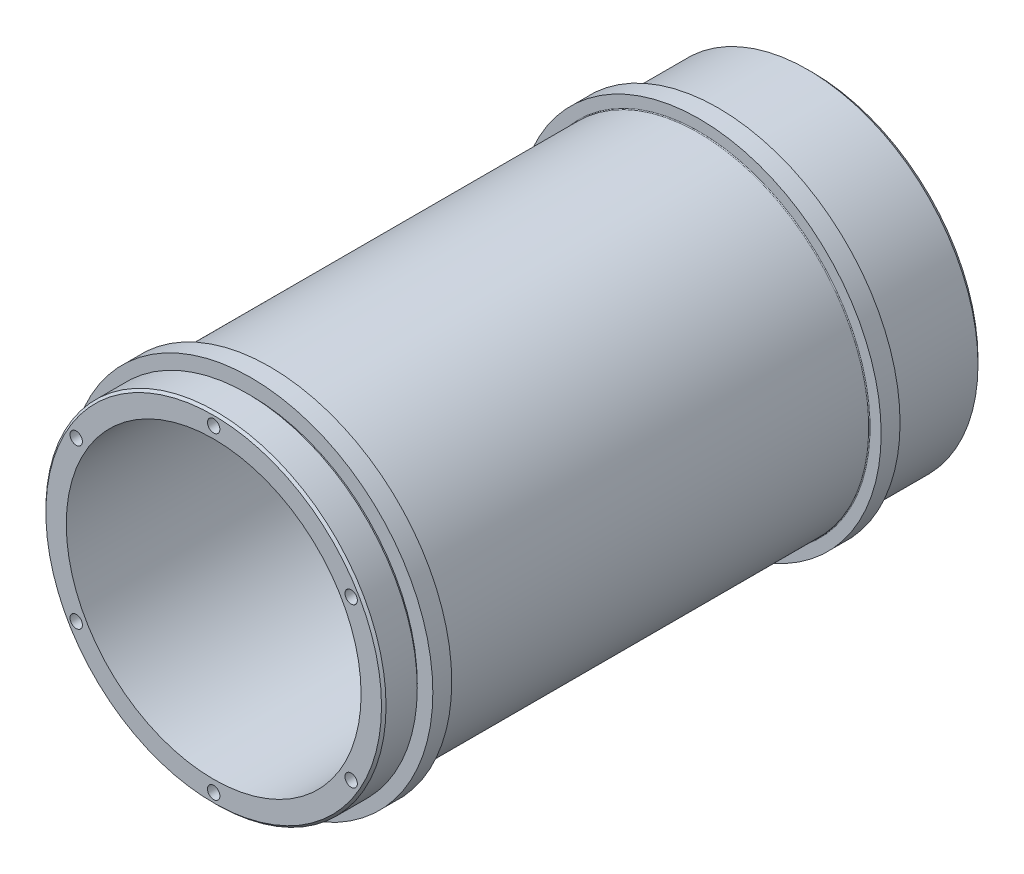
SolidWorks part; units mm, degrees
ref_plane "Front Plane" through (0, 0, 0) normal (0, 0, 1) x (1, 0, 0)
ref_plane "Top Plane" through (0, 0, 0) normal (0, 1, 0) x (1, 0, 0)
ref_plane "Right Plane" through (0, 0, 0) normal (1, 0, 0) x (0, 0, -1)
sketch "Sketch1" plane through (0, 0, 0) normal (0, 0, 1) x (1, 0, 0)
  circle A0 centre (0, 0) radius 57.15
  dimension "D1" = 114.3
extrude "Boss-Extrude1" add sketch "Sketch1" along normal blind 201.2442
ref_plane "Plane1" through (0, 0, 201.2442) normal (0, 0, 1) x (1, 0, 0)
sketch "Sketch3" plane through (0, 0, 0) normal (1, 0, 0) x (0, 0, -1)
  line L0 (0, 57.15) -> (-201.2442, 57.15) construction
  line L1 (-31.75, 57.15) -> (-30.48, 57.15)
  line L2 (-31.75, 57.15) -> (-31.75, 55.88)
  line L3 (-31.75, 55.88) -> (-30.48, 55.88)
  line L4 (-30.48, 57.15) -> (-30.48, 55.88)
  line L5 (0, 55) -> (0, -55) construction
  line L7 (-189.992, 57.15) -> (-188.722, 57.15)
  line L8 (-189.992, 57.15) -> (-189.992, 55.88)
  line L9 (-189.992, 55.88) -> (-188.722, 55.88)
  line L10 (-188.722, 57.15) -> (-188.722, 55.88)
  line L11 (-212.826, 0) -> (0, 0) construction
  dimension "D1" = 1.27
  dimension "D2" = 1.27
  dimension "D3" = 31.75
  dimension "D4" = 1.27
  dimension "D5" = 1.27
  dimension "D6" = 156.972
revolve "Cut-Revolve2" cut sketch "Sketch3" angle 360 about L11
ref_plane "Plane4" through (0, 0, 188.722) normal (0, 0, 1) x (1, 0, 0)
sketch "Sketch9" plane through (0, 0, 188.722) normal (0, 0, 1) x (1, 0, 0)
  circle A0 centre (0, 0) radius 61.1124
  dimension "D1" = 122.2248
extrude "Boss-Extrude4" add sketch "Sketch9" against normal blind 6.35
ref_plane "Plane5" through (0, 0, 31.75) normal (0, 0, -1) x (-1, 0, 0)
sketch "Sketch10" plane through (0, 0, 31.75) normal (0, 0, -1) x (-1, 0, 0)
  circle A0 centre (0, 0) radius 61.1124
extrude "Boss-Extrude5" add sketch "Sketch10" against normal blind 6.35
hole_wizard "#97 (0.164) Diameter Hole1" positions "Sketch11" profile "Sketch12" hole size "#97" standard "ANSI Inch"
sketch "Sketch11" plane through (0, 0, 201.2442) normal (0, 0, 1) x (1, 0, 0)
  line L0 (0, -62.865) -> (0, 62.865) construction
  point P0 (0, 53.34)
  point P12 (46.1938, 26.67)
  point P13 (46.1938, -26.67)
  point P14 (0, -53.34)
  point P15 (-46.1938, -26.67)
  point P16 (-46.1938, 26.67)
  point P18 (0, 0)
  dimension "D1" = 53.34
  dimension "D2" = 6
sketch "Sketch12" plane through (0, 53.34, 201.2442) normal (1, 0, 0) x (0, -1, 0)
  line L0 (0, 0) -> (0, 9.5065)
  line L1 (0, 9.5065) -> (2.0828, 8.255)
  line L2 (2.0828, 8.255) -> (2.0828, 0)
  line L5 (2.0828, 0) -> (0, 0)
  line L10 (0, 9.5065) -> (-2.0828, 8.255) construction
  line L11 (0, -6.35) -> (0, 107.95) construction
  dimension "Hole Dia." = 4.1656
  dimension "Hole Depth" = 8.255
  dimension "Drill Angle" = 118
hole_wizard "#97 (0.352) Diameter Hole1" positions "Sketch16" profile "Sketch17" hole size "#97" standard "ANSI Inch" end condition through all
sketch "Sketch16" plane through (0, 0, 201.2442) normal (0, 0, 1) x (1, 0, 0)
  line L0 (0, -62.865) -> (0, 62.865) construction
  line L1 (62.865, 0) -> (-62.865, 0) construction
  point P9 (0, 38.735)
  point P20 (33.5455, 19.3675)
  point P21 (33.5455, -19.3675)
  point P22 (0, -38.735)
  point P23 (-33.5455, -19.3675)
  point P24 (-33.5455, 19.3675)
  point P30 (0, 0)
  dimension "D1" = 38.735
  dimension "D2" = 6
sketch "Sketch17" plane through (0, 38.735, 201.2442) normal (1, 0, 0) x (0, -1, 0)
  line L0 (0, 0) -> (0, 201.2442)
  line L1 (0, 201.2442) -> (4.4704, 201.2442)
  line L2 (4.4704, 201.2442) -> (4.4704, 0)
  line L5 (4.4704, 0) -> (0, 0)
  line L11 (0, -6.35) -> (0, 107.95) construction
  dimension "Thru Hole Dia." = 8.9408
  dimension "Thru Hole Depth" = 201.2442
sketch "Sketch18" plane through (0, 0, 201.2442) normal (0, 0, 1) x (1, 0, 0)
  line L0 (-915.5188, -528.575) -> (-33.5455, -19.3675) construction
  line L1 (62.865, 0) -> (-62.865, 0) construction
  line L2 (-3.3488, 10.4902) -> (70.9835, 10.4902) construction
  line L3 (0, 0) -> (59.0953, 34.1187) construction
  line L4 (0, 0) -> (112.8605, 0) construction
  line L5 (26.5798, 10.4902) -> (32.1193, 10.4902)
  line L6 (22.3747, 17.7737) -> (25.1444, 22.571)
  line L7 (26.5798, -10.4902) -> (32.1193, -10.4902)
  line L8 (22.3747, -17.7737) -> (25.1444, -22.571)
  line L9 (4.2051, -28.2639) -> (6.9749, -33.0612)
  line L10 (-4.2051, -28.2639) -> (-6.9749, -33.0612)
  line L11 (-22.3747, -17.7737) -> (-25.1444, -22.571)
  line L12 (-26.5798, -10.4902) -> (-32.1193, -10.4902)
  line L13 (-26.5798, 10.4902) -> (-32.1193, 10.4902)
  line L14 (-22.3747, 17.7737) -> (-25.1444, 22.571)
  line L15 (-4.2051, 28.2639) -> (-6.9749, 33.0612)
  line L16 (4.2051, 28.2639) -> (6.9749, 33.0612)
  arc A0 (26.5798, 10.4902) -> (22.3747, 17.7737) centre (0, 0) ccw
  arc A1 (38.735, 0) -> (38.4172, 4.952) centre (0, 0) ccw
  arc A2 (38.4172, 4.952) -> (32.1193, 10.4902) centre (32.1193, 4.1402) ccw
  arc A3 (19.3675, 33.5455) -> (23.4971, 30.7942) centre (0, 0) cw
  arc A4 (23.4971, 30.7942) -> (25.1444, 22.571) centre (19.6451, 25.746) cw
  arc A5 (38.735, 0) -> (38.4172, -4.952) centre (0, 0) cw
  arc A6 (38.4172, -4.952) -> (32.1193, -10.4902) centre (32.1193, -4.1402) cw
  arc A7 (22.3747, -17.7737) -> (26.5798, -10.4902) centre (0, 0) ccw
  arc A8 (23.4971, -30.7942) -> (25.1444, -22.571) centre (19.6451, -25.746) ccw
  arc A9 (19.3675, -33.5455) -> (23.4971, -30.7942) centre (0, 0) ccw
  arc A10 (19.3675, -33.5455) -> (14.92, -35.7462) centre (0, 0) cw
  arc A11 (14.92, -35.7462) -> (6.9749, -33.0612) centre (12.4741, -29.8862) cw
  arc A12 (-4.2051, -28.2639) -> (4.2051, -28.2639) centre (0, 0) ccw
  arc A13 (-14.92, -35.7462) -> (-6.9749, -33.0612) centre (-12.4741, -29.8862) ccw
  arc A14 (-19.3675, -33.5455) -> (-14.92, -35.7462) centre (0, 0) ccw
  arc A15 (-19.3675, -33.5455) -> (-23.4971, -30.7942) centre (0, 0) cw
  arc A16 (-23.4971, -30.7942) -> (-25.1444, -22.571) centre (-19.6451, -25.746) cw
  arc A17 (-26.5798, -10.4902) -> (-22.3747, -17.7737) centre (0, 0) ccw
  arc A18 (-38.4172, -4.952) -> (-32.1193, -10.4902) centre (-32.1193, -4.1402) ccw
  arc A19 (-38.735, 0) -> (-38.4172, -4.952) centre (0, 0) ccw
  arc A20 (-38.735, 0) -> (-38.4172, 4.952) centre (0, 0) cw
  arc A21 (-38.4172, 4.952) -> (-32.1193, 10.4902) centre (-32.1193, 4.1402) cw
  arc A22 (-22.3747, 17.7737) -> (-26.5798, 10.4902) centre (0, 0) ccw
  arc A23 (-23.4971, 30.7942) -> (-25.1444, 22.571) centre (-19.6451, 25.746) ccw
  arc A24 (-19.3675, 33.5455) -> (-23.4971, 30.7942) centre (0, 0) ccw
  arc A25 (-19.3675, 33.5455) -> (-14.92, 35.7462) centre (0, 0) cw
  arc A26 (-14.92, 35.7462) -> (-6.9749, 33.0612) centre (-12.4741, 29.8862) cw
  arc A27 (4.2051, 28.2639) -> (-4.2051, 28.2639) centre (0, 0) ccw
  arc A28 (14.92, 35.7462) -> (6.9749, 33.0612) centre (12.4741, 29.8862) ccw
  arc A29 (19.3675, 33.5455) -> (14.92, 35.7462) centre (0, 0) ccw
  point P16 (37.2875, 10.4902)
  point P74 (0, 0)
  dimension "D1" = 57.15
  dimension "D2" = 77.47
  dimension "D5" = 6.35
  dimension "D3" = 30
  dimension "D4" = 10.4902
  dimension "D6" = 6
extrude "Cut-Extrude3" cut sketch "Sketch18" against normal through all
sketch "Sketch20" plane through (0, 0, 201.2442) normal (0, 0, 1) x (1, 0, 0)
  circle A0 centre (0, 0) radius 49.53
extrude "Cut-Extrude4" cut sketch "Sketch20" against normal blind 191.7192
fillet "Fillet4" radius 0.508 1 edges at (49.53, 0, 9.525)
fillet "Fillet5" radius 0.254 2 edges at (-57.15, 0, 38.1) (57.15, 0, 182.372)
chamfer "Chamfer1" distance 0.762 angle 45 1 edges at (57.15, 0, 201.2442)
chamfer "Chamfer2" distance 1.6002 angle 45 1 edges at (57.15, 0, 0)
